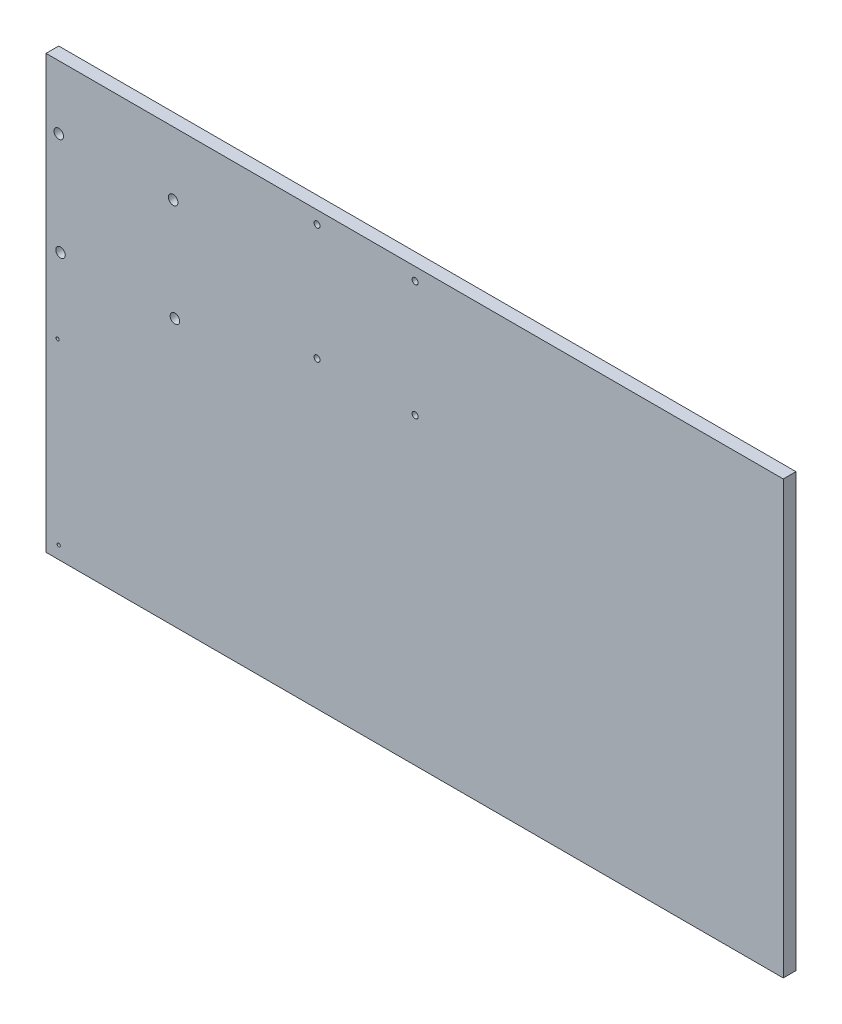
SolidWorks part; units mm, degrees
ref_plane "Front Plane" through (0, 0, 0) normal (1, 0, 0) x (0, 1, 0)
ref_plane "Top Plane" through (0, 0, 0) normal (0, 0, 1) x (0, 1, 0)
ref_plane "Right Plane" through (0, 0, 0) normal (0, 1, 0) x (-1, 0, 0)
sketch "Sketch1" plane through (0, 0, 0) normal (0, 0, 1) x (0, 1, 0)
  line L1 (0, 0) -> (215.9, 0)
  line L2 (0, 0) -> (0, 215.9)
  line L3 (0, 215.9) -> (215.9, 215.9)
  line L4 (215.9, 0) -> (215.9, 215.9)
  dimension "D1" = 215.9
  dimension "D2" = 215.9
extrude "Boss-Extrude1" add sketch "Sketch1" along normal blind 6.35
sketch "Sketch2" plane through (0, 0, 6.35) normal (0, 0, 1) x (1, 0, 0)
  line L0 (-215.9, 0) -> (0, 0) construction
  line L1 (-215.9, 215.9) -> (-215.9, 0) construction
  circle A0 centre (-209.55, 6.35) radius 0.7988
  circle A1 centre (-210.1144, 95.2482) radius 0.7988
  dimension "D1" = 1.5977
  dimension "D2" = 1.5977
  dimension "D3" = 88.9
  dimension "D4" = 6.35
  dimension "D5" = 6.35
extrude "Cut-Extrude1" cut sketch "Sketch2" against normal through all
sketch "Sketch3" plane through (0, 0, 6.35) normal (0, 0, 1) x (1, 0, 0)
  line L1 (-215.9, 215.9) -> (-215.9, 0) construction
  circle A0 centre (-209.55, 184.3033) radius 2.3749
  circle A1 centre (-208.6605, 133.3482) radius 2.3749
  circle A2 centre (-152.4, 184.2799) radius 2.3749
  circle A3 centre (-151.5105, 133.35) radius 2.3749
  circle A4 centre (-210.1144, 95.2482) radius 0.7988 construction
  dimension "D1" = 4.7498
  dimension "D2" = 4.7498
  dimension "D3" = 4.7498
  dimension "D4" = 4.7498
  dimension "D8" = 6.35
  dimension "D9" = 38.1
  dimension "D5" = 57.15
  dimension "D6" = 57.15
  dimension "D7" = 50.9551
extrude "Cut-Extrude2" cut sketch "Sketch3" against normal through all
sketch "Sketch4" plane through (0, 0, 6.35) normal (0, 0, 1) x (1, 0, 0)
  line L0 (0, 215.9) -> (-215.9, 215.9) construction
  circle A0 centre (-80.5122, 209.55) radius 1.4986
  circle A1 centre (-31.5156, 209.55) radius 1.4986
  circle A2 centre (-152.4, 184.2799) radius 2.3749 construction
  circle A3 centre (-80.5122, 151.5618) radius 1.4986
  circle A4 centre (-31.5156, 151.5618) radius 1.4986
  dimension "D1" = 48.9966
  dimension "D2" = 76.2
  dimension "D3" = 57.9882
  dimension "D4" = 57.9882
  dimension "D5" = 2.9972
  dimension "D6" = 2.9972
  dimension "D7" = 2.9972
  dimension "D8" = 2.9972
  dimension "D9" = 6.35
  dimension "D10" = 0
  dimension "D11" = 0
extrude "Cut-Extrude4" cut sketch "Sketch4" against normal through all
sketch "Sketch5" plane through (0, 0, 0) normal (1, 0, 0) x (0, 1, 0)
  line L1 (0, 6.35) -> (215.9, 6.35)
  line L2 (0, 6.35) -> (0, 0)
  line L3 (0, 0) -> (215.9, 0)
  line L4 (215.9, 6.35) -> (215.9, 0)
extrude "Boss-Extrude2" add sketch "Sketch5" along normal blind 152.4
